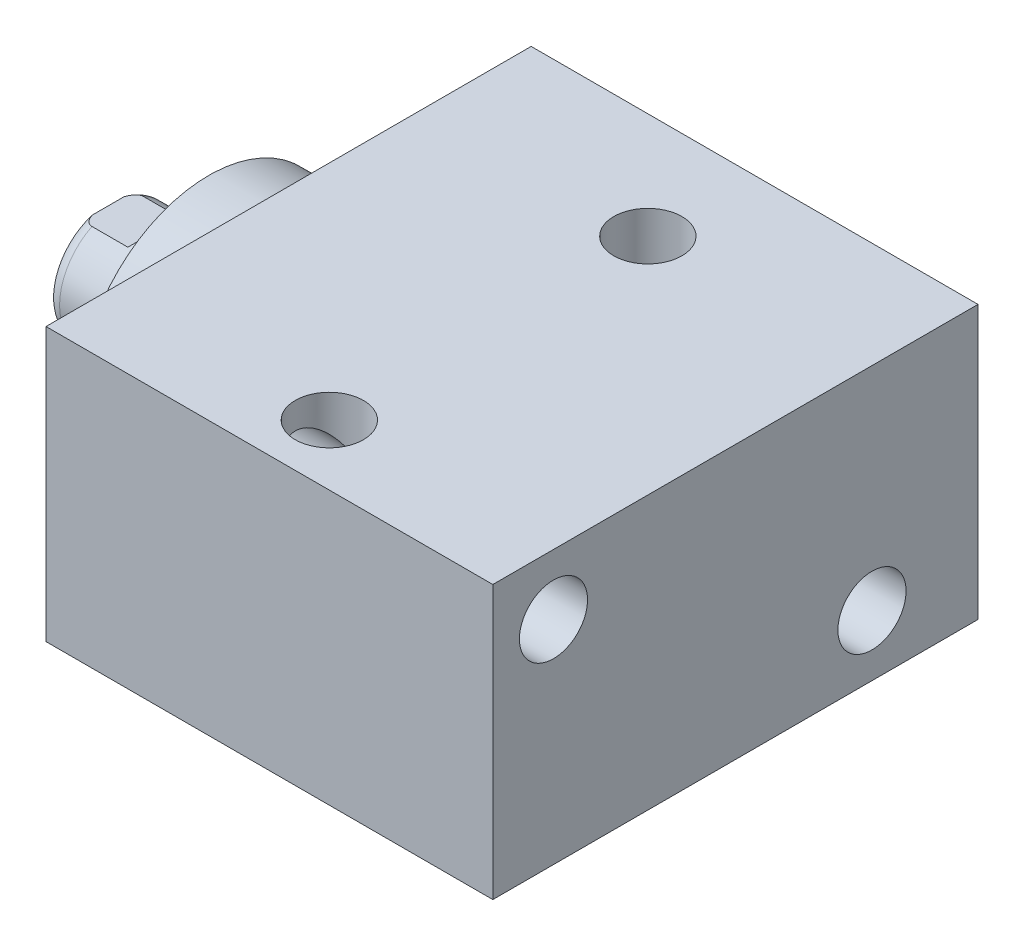
SolidWorks part; units mm, degrees
material "Alloy Steel"
ref_plane "Front Plane" through (0, 0, 0) normal (0, 0, 1) x (1, 0, 0)
ref_plane "Top Plane" through (0, 0, 0) normal (0, 1, 0) x (1, 0, 0)
ref_plane "Right Plane" through (0, 0, 0) normal (1, 0, 0) x (0, 0, -1)
ref_plane "Plane1" through (0, 0, 0) normal (1, 0, 0) x (0, 0, -1)
sketch "Sketch1" plane through (0, 0, 0) normal (1, 0, 0) x (0, 0, -1)
  line L0 (-23.0124, 14.2875) -> (27.7876, 14.2875)
  line L1 (27.7876, 14.2875) -> (27.7876, -14.2875)
  line L2 (27.7876, -14.2875) -> (-23.0124, -14.2875)
  line L3 (-23.0124, -14.2875) -> (-23.0124, 14.2875)
  line L4 (0, -24.4475) -> (0, 24.4475) construction
  dimension "D1" = 28.575
  dimension "D2" = 14.2875
  dimension "D3" = 50.8
  dimension "D4" = 23.0124
extrude "Extrude1" add sketch "Sketch1" along normal blind 46.7868
ref_plane "Plane12" through (0, 4.7625, 0) normal (0, 1, 0) x (-1, 0, 0)
sketch "S2D0002" plane through (0, 4.7625, 0) normal (0, 1, 0) x (-1, 0, 0)
  line L0 (-14.5415, -27.5336) -> (-18.161, -27.5336)
  line L1 (-14.5415, -27.5082) -> (-14.5415, -27.5336)
  line L2 (-14.5415, -27.5082) -> (-13.9446, -26.9113)
  line L3 (-13.9446, -26.9113) -> (-13.9446, -14.0716)
  line L4 (-13.9446, -14.0716) -> (-9.525, -14.0716)
  line L5 (-9.525, -14.0716) -> (-9.525, -27.7876)
  line L6 (-9.525, -19.1384) -> (-9.525, 0.6985) construction
  line L7 (0, -27.7876) -> (0, 23.0124) construction
  line L8 (-18.161, -27.7876) -> (-18.161, -27.5336)
  line L9 (-46.7868, -27.7876) -> (0, -27.7876) construction
  line L10 (-18.161, -27.7876) -> (-9.525, -27.7876)
  dimension "D1" = 13.716
  dimension "D2" = 9.525
  dimension "D3" = 8.8392
  dimension "D4" = 45
  dimension "D5" = 0.6223
  dimension "D6" = 10.033
  dimension "D7" = 0.0254
  dimension "D8" = 0.254
  dimension "D9" = 17.272
revolve "Cut-Revolve1" cut sketch "S2D0002" angle 360 about L6
pattern_linear "LPattern1" count 2 spacing 27.94 along (1, 0, 0) of "Cut-Revolve1"
sketch "Sketch5" plane through (0, 0, 0) normal (-1, 0, 0) x (0, 0, 1)
  circle A0 centre (0, 0) radius 13.5001
  dimension "D1" = 27.0002
extrude "Extrude2" add sketch "Sketch5" along normal blind 5.969
ref_plane "Plane5" through (0, 0, 0) normal (0, -1, 0) x (0, 0, 1)
sketch "Sketch6" plane through (0, 0, 0) normal (0, -1, 0) x (0, 0, 1)
  line L0 (0, 5.969) -> (-6.3373, 5.969)
  line L1 (-6.3373, 5.969) -> (-6.3373, 16.51)
  line L2 (-6.3373, 16.51) -> (0, 16.51)
  line L3 (0, 16.51) -> (0, 5.969)
  line L4 (0, -5.7546) -> (0, 21.1709) construction
  line L5 (13.5001, 5.969) -> (-13.5001, 5.969) construction
  line L6 (23.0124, -46.7868) -> (-27.7876, -46.7868) construction
  dimension "D1" = 63.2968
  dimension "D2" = 12.6746
revolve "Revolve1" add sketch "Sketch6" angle 360 about L4
ref_plane "Plane6" through (-18.5113, 3.2639, 0) normal (0, 0, 1) x (0, 1, 0)
sketch "S2D0001" plane through (-18.5113, 3.2639, 0) normal (0, 0, 1) x (0, 1, 0)
  line L0 (-0.7493, -3.3651) -> (-0.7493, -18.0033)
  line L1 (-3.2639, -19.5142) -> (-0.7493, -18.0033)
  line L2 (0.0381, -2.0013) -> (-3.2639, -2.0013)
  line L3 (-3.2639, -2.0013) -> (-3.2639, -19.5142)
  line L4 (-0.7493, -3.3651) -> (0.0381, -2.0013)
  line L5 (-3.2639, -18.5113) -> (-3.2639, 2.765) construction
  line L6 (3.0734, -2.0013) -> (-9.6012, -2.0013) construction
  dimension "D1" = 30
  dimension "D2" = 6.604
  dimension "D3" = 5.0292
  dimension "D4" = 16.002
  dimension "D5" = 59
revolve "Cut-Revolve4" cut sketch "S2D0001" angle 360 about L5
ref_plane "Plane7" through (0, 0, 0) normal (0, 1, 0) x (0, 0, -1)
sketch "Sketch8" plane through (0, 0, 0) normal (0, 1, 0) x (0, 0, -1)
  line L0 (-6.3373, 10.1854) -> (-6.096, 10.9474)
  line L1 (-6.096, 10.9474) -> (-6.096, 15.494)
  line L2 (0, 12.6594) -> (0, 20.8178) construction
  line L3 (-6.3373, 10.1854) -> (-6.3373, 16.51)
  line L4 (-5.7079, 16.51) -> (-6.3373, 16.51)
  line L5 (6.3373, 16.51) -> (-6.3373, 16.51) construction
  line L6 (-6.3373, 16.51) -> (-6.3373, 5.969) construction
  arc A0 (-5.7079, 16.51) -> (-6.096, 15.494) centre (-4.572, 15.494) ccw
  dimension "D2" = 1.524
  dimension "D1" = 12.192
  dimension "D3" = 1.016
  dimension "D4" = 0.762
  dimension "D5" = 5.5626
revolve "Cut-Revolve5" cut sketch "Sketch8" angle 360 about L2
ref_plane "Plane11" through (0, 0, 0) normal (0, 0, -1) x (0, -1, 0)
sketch "Sketch12" plane through (0, 0, 0) normal (0, 0, -1) x (0, -1, 0)
  line L0 (5.461, 16.51) -> (5.461, 11.7348)
  line L1 (5.461, 11.7348) -> (6.096, 11.0998)
  line L2 (-5.461, 16.51) -> (-5.461, 11.7348)
  line L3 (-5.461, 11.7348) -> (-6.096, 11.0998)
  line L4 (5.461, 16.51) -> (6.096, 16.51)
  line L5 (0, 13.7262) -> (0, 20.767) construction
  line L6 (-6.096, 11.0998) -> (-6.096, 16.51)
  line L8 (6.096, 10.9474) -> (6.096, 15.494) construction
  line L9 (6.096, 11.0998) -> (6.096, 16.51)
  line L10 (-5.461, 16.51) -> (-6.096, 16.51)
  line L12 (5.7079, 16.51) -> (-5.7079, 16.51) construction
  dimension "D1" = 10.922
  dimension "D2" = 4.7752
  dimension "D3" = 45
extrude "Cut-Extrude4" cut sketch "Sketch12" against normal mid plane 60.96
hole_wizard "Hole1" positions "Sketch15" profile "Sketch14" legacy end condition up to next
sketch "Sketch15" plane through (0, 0, 0) normal (-1, 0, 0) x (0, 0, 1)
  line L0 (0, 0) -> (-29.9914, 0) construction
  line L1 (0, 0) -> (0, 25.7648) construction
  point P0 (-16.6878, -7.9248)
  point P11 (16.6624, 7.9502)
  dimension "D1" = 7.9248
  dimension "D2" = 16.6878
  dimension "D3" = 15.875
  dimension "D4" = 33.3502
sketch "Sketch14" plane through (0, -7.9248, -16.6878) normal (0, 1, 0) x (0, 0, 1)
  line L0 (0, 0) -> (0, 46.7868)
  line L1 (0, 46.7868) -> (3.5685, 46.7868)
  line L2 (3.5685, 46.7868) -> (3.5685, 0)
  line L3 (3.5685, 0) -> (0, 0)
  line L4 (0, 110) -> (0, -10) construction
  dimension "Diameter" = 7.137
  dimension "Depth" = 46.7868
hole_wizard "Hole2" positions "Sketch17" profile "Sketch16" legacy
sketch "Sketch17" plane through (0, 14.2875, 0) normal (0, 1, 0) x (-1, 0, 0)
  line L0 (0, 0) -> (-59.3363, 0) construction
  line L1 (0, -27.7876) -> (0, 23.0124) construction
  point P0 (-23.3172, -16.6878)
  point P9 (-23.3172, 16.6624)
  dimension "D1" = 33.3502
  dimension "D2" = 23.3172
  dimension "D3" = 16.6878
sketch "Sketch16" plane through (23.3172, 14.2875, -16.6878) normal (1, 0, 0) x (0, 0, 1)
  line L0 (0, 0) -> (0, 28.575)
  line L1 (0, 28.575) -> (3.5685, 28.575)
  line L2 (3.5685, 28.575) -> (3.5685, 0)
  line L3 (3.5685, 0) -> (0, 0)
  line L4 (0, 110) -> (0, -10) construction
  dimension "Diameter" = 7.137
  dimension "Depth" = 28.575
